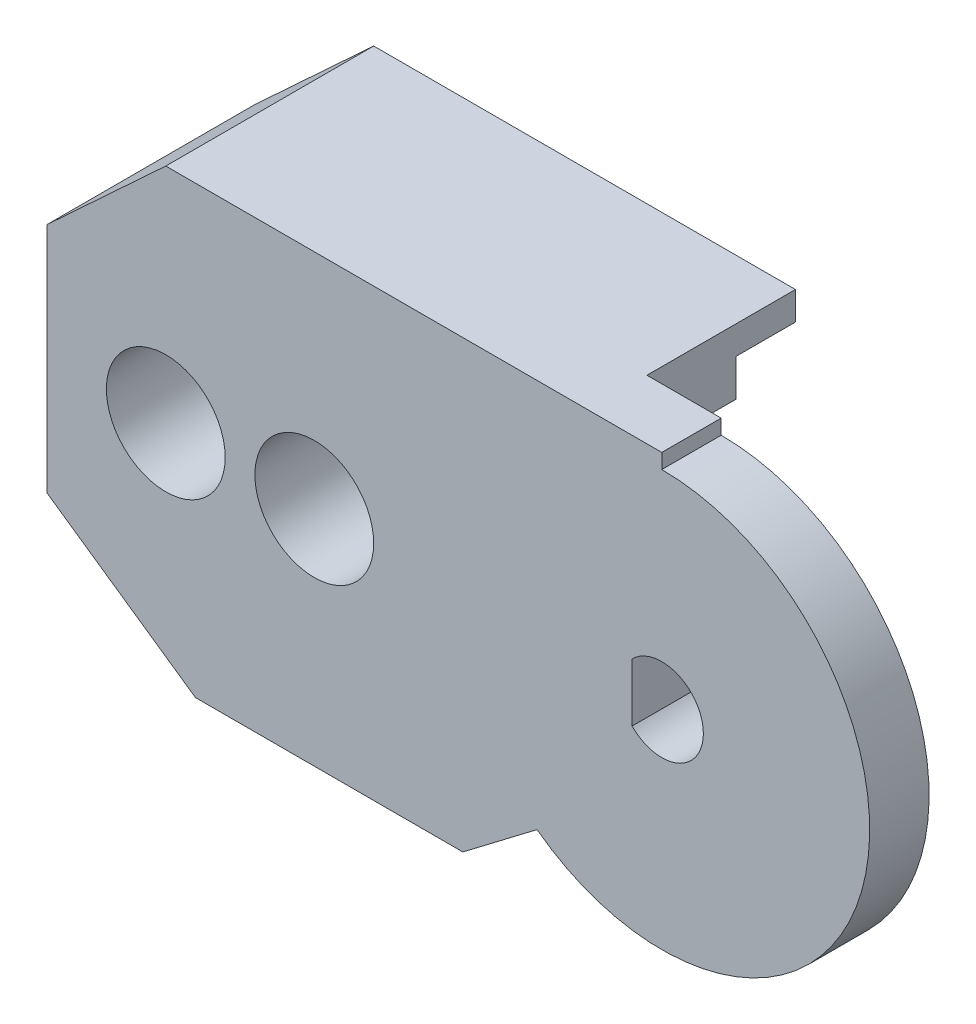
SolidWorks part; units mm, degrees
ref_plane "Front Plane" through (0, 0, 0) normal (0, 0, 1) x (1, 0, 0)
ref_plane "Top Plane" through (0, 0, 0) normal (0, 1, 0) x (1, 0, 0)
ref_plane "Right Plane" through (0, 0, 0) normal (1, 0, 0) x (0, 0, -1)
sketch "Sketch1" plane through (0, 0, 0) normal (0, 0, 1) x (1, 0, 0)
  line L2 (-20.7, 3.7934) -> (-20.7, -4.0316)
  line L3 (-15.7, -7.5) -> (-6.7, -7.5)
  line L4 (-6.7, -7.5) -> (-4.2, -5.6)
  line L7 (0, 7) -> (0, 7.5)
  line L8 (-20.7, 3.7934) -> (-16.7, 7.5)
  line L9 (-20.7, -4.0316) -> (-15.7, -7.5)
  line L10 (0, 7.5) -> (-16.7, 7.5)
  arc A1 (-4.2, -5.6) -> (7, 0) centre (0, 0) ccw
  arc A2 (7, 0) -> (0, 7) centre (0, 0) ccw
  dimension "D1" = 7
  dimension "D2" = 4
  dimension "D3" = 5
  dimension "D4" = 16.7
  dimension "D7" = 2.5
  dimension "D8" = 14
  dimension "D9" = 3.4684
  dimension "D10" = 1.9
  dimension "D11" = 7.8251
extrude "Boss-Extrude1" add sketch "Sketch1" along normal blind 2
sketch "Sketch2" plane through (0, 0, 0) normal (0, 0, -1) x (-1, 0, 0)
  line L0 (16.7, 7.5) -> (20.7, 3.7934)
  line L1 (20.7, 3.7934) -> (20.7, -4.0316)
  line L2 (20.7, -4.0316) -> (15.7, -7.5)
  line L3 (15.7, -7.5) -> (6.7, -7.5)
  line L4 (6.7, -7.5) -> (6.7, -4.5)
  line L5 (16.7, 7.5) -> (2.5, 7.5)
  line L6 (0, 7.5) -> (16.7, 7.5) construction
  line L7 (2.5, 7.5) -> (2.5, 5.3)
  line L8 (2.5, 5.3) -> (5.5, 5.3)
  line L9 (5.5, 5.3) -> (5.5, 2)
  line L10 (5.5, 2) -> (7.7, 2)
  line L11 (7.7, 2) -> (7.7, -4.5)
  line L12 (7.7, -4.5) -> (6.7, -4.5)
  dimension "D1" = 2.5
  dimension "D2" = 3
  dimension "D3" = 13
  dimension "D4" = 2.2
  dimension "D5" = 3.3
  dimension "D6" = 3
extrude "Boss-Extrude2" add sketch "Sketch2" along normal blind 5
sketch "Sketch4" plane through (0, 0, 0) normal (0, 0, -1) x (-1, 0, 0)
  circle A0 centre (0, 0) radius 3.9
  dimension "D1" = 7.8
extrude "Boss-Extrude3" add sketch "Sketch4" along normal blind 1.2
sketch "Sketch5" plane through (0, 0, -1.2) normal (0, 0, -1) x (-1, 0, 0)
  line L0 (1, 0.9798) -> (1, -0.9798)
  arc A0 (1, 0.9798) -> (1, -0.9798) centre (0, 0) ccw
  dimension "D1" = 1
  dimension "D2" = 2.8
extrude "Cut-Extrude1" cut sketch "Sketch5" against normal blind 5
sketch "Sketch6" plane through (0, 0, -5) normal (0, 0, -1) x (-1, 0, 0)
  line L0 (7.8929, -7.5) -> (3.2667, 2.4201) construction
  line L1 (6.7, -7.5) -> (15.7, -7.5) construction
sketch "Sketch7" plane through (0, -7.5, 0) normal (0, -1, 0) x (1, 0, 0)
  line L2 (-6.7, -5) -> (-15.7, -5) construction
  line L3 (-8.4342, -5.75) -> (-9.9342, -5.75)
  line L4 (-8.4342, -5.75) -> (-8.4342, -4.25)
  line L5 (-8.4342, -4.25) -> (-9.9342, -4.25)
  line L6 (-9.9342, -5.75) -> (-9.9342, -4.25)
  line L7 (-8.4342, -5.75) -> (-9.9342, -4.25) construction
  line L8 (-8.4342, -4.25) -> (-9.9342, -5.75) construction
  point P0 (-9.1842, -5)
  dimension "D1" = 1.5
  dimension "D2" = 1.5
extrude "Cut-Extrude2" cut sketch "Sketch7" along direction (0.4227, 0.9063, 0) on the side against the normal blind 5
sketch "Sketch8" plane through (0, 0, -5) normal (0, 0, -1) x (-1, 0, 0)
  line L0 (20.7, -4.0316) -> (20.7, 3.7934) construction
  line L1 (7.7, 2) -> (7.7, -2.9685) construction
  line L2 (16.7, 7.5) -> (2.5, 7.5) construction
  circle A0 centre (16.7, 0) radius 0.95
  circle A1 centre (11.7, 0) radius 0.95
  dimension "D1" = 4
  dimension "D5" = 1.9
  dimension "D6" = 1.9
  dimension "D2" = 5
  dimension "D3" = 4
  dimension "D4" = 7.5
extrude "Cut-Extrude3" cut sketch "Sketch8" against normal blind 8
sketch "Sketch9" plane through (0, 0, 2) normal (0, 0, 1) x (1, 0, 0)
  circle A0 centre (-16.7, 0) radius 2
  circle A1 centre (-11.7, 0) radius 2
extrude "Cut-Extrude4" cut sketch "Sketch9" against normal blind 3
sketch "Sketch10" plane through (0, 0, -5) normal (0, 0, -1) x (-1, 0, 0)
  line L0 (2.5, 5.3) -> (5.5, 5.3)
  line L1 (2.5, 5.3) -> (2.5, 6.55)
  line L2 (5.5, 5.3) -> (5.5, 6.55)
  line L3 (2.5, 6.55) -> (5.5, 6.55)
  dimension "D1" = 1.25
extrude "Cut-Extrude5" cut sketch "Sketch10" against normal blind 2
